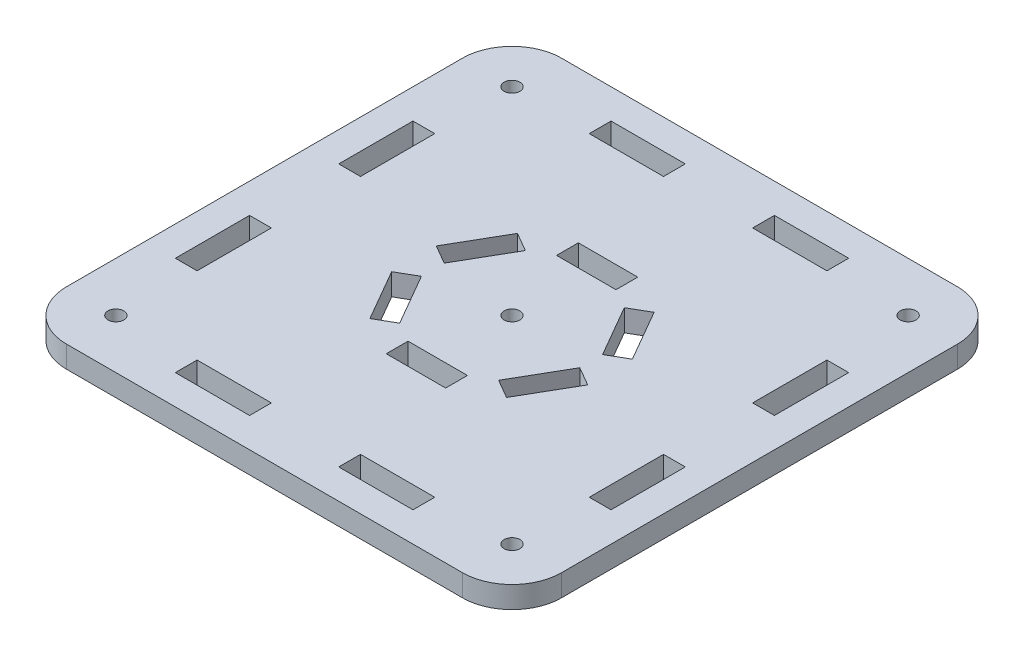
SolidWorks part; units mm, degrees
ref_plane "前视基准面" through (0, 0, 0) normal (0, 0, 1) x (1, 0, 0)
ref_plane "上视基准面" through (0, 0, 0) normal (0, 1, 0) x (1, 0, 0)
ref_plane "右视基准面" through (0, 0, 0) normal (1, 0, 0) x (0, 0, -1)
sketch "草图1" plane through (0, 0, 0) normal (0, 1, 0) x (1, 0, 0)
  line L1 (-50, -50) -> (50, -50)
  line L2 (-50, -50) -> (-50, 50)
  line L3 (-50, 50) -> (50, 50)
  line L4 (50, -50) -> (50, 50)
  line L5 (0, 50) -> (0, -50) construction
  line L6 (-50, 0) -> (50, 0) construction
  circle A0 centre (0, 0) radius 1.6
  point P0 (0, 0)
  dimension "D3" = 3.2
  dimension "D1" = 100
  dimension "D2" = 100
extrude "凸台-拉伸1" add sketch "草图1" along normal blind 4.4
fillet "圆角1" radius 10 4 edges at (50, 2.2, 50) (-50, 2.2, 50) (50, 2.2, -50) (-50, 2.2, -50)
sketch "草图2" plane through (0, 4.4, 0) normal (0, 1, 0) x (1, 0, 0)
  line L0 (0, 50) -> (0, 0) construction
  line L1 (40, 50) -> (-40, 50) construction
  line L2 (-24, 44) -> (-24, 39.6)
  line L3 (9, 44) -> (24, 44)
  line L4 (9, 44) -> (9, 39.6)
  line L5 (9, 39.6) -> (24, 39.6)
  line L6 (24, 44) -> (24, 39.6)
  line L7 (-9, 39.6) -> (-24, 39.6)
  line L8 (-9, 44) -> (-9, 39.6)
  line L9 (-9, 44) -> (-24, 44)
  line L10 (44, -9) -> (39.6, -9)
  line L11 (44, -9) -> (44, -24)
  line L12 (39.6, -9) -> (39.6, -24)
  line L13 (44, -24) -> (39.6, -24)
  line L14 (44, 9) -> (44, 24)
  line L15 (44, 24) -> (39.6, 24)
  line L16 (39.6, 9) -> (39.6, 24)
  line L17 (44, 9) -> (39.6, 9)
  line L18 (-9, -44) -> (-9, -39.6)
  line L19 (-9, -44) -> (-24, -44)
  line L20 (-9, -39.6) -> (-24, -39.6)
  line L21 (-24, -44) -> (-24, -39.6)
  line L22 (9, -44) -> (24, -44)
  line L23 (24, -44) -> (24, -39.6)
  line L24 (9, -39.6) -> (24, -39.6)
  line L25 (9, -44) -> (9, -39.6)
  line L26 (-44, 9) -> (-39.6, 9)
  line L27 (-44, 9) -> (-44, 24)
  line L28 (-39.6, 9) -> (-39.6, 24)
  line L29 (-44, 24) -> (-39.6, 24)
  line L30 (-44, -9) -> (-44, -24)
  line L31 (-44, -24) -> (-39.6, -24)
  line L32 (-39.6, -9) -> (-39.6, -24)
  line L33 (-44, -9) -> (-39.6, -9)
  circle A0 centre (40, 40) radius 1.6
  circle A1 centre (40, -40) radius 1.6
  circle A2 centre (-40, -40) radius 1.6
  circle A3 centre (-40, 40) radius 1.6
  point P40 (0, 0)
  point P50 (0, 0)
  dimension "D6" = 3.2
  dimension "D1" = 4.4
  dimension "D2" = 18
  dimension "D3" = 15
  dimension "D4" = 6
  dimension "D5" = 4
  dimension "D7" = 4
extrude "切除-拉伸1" cut sketch "草图2" against normal up to next
sketch "草图3" plane through (0, 4.4, 0) normal (0, 1, 0) x (1, 0, 0)
  line L0 (0, 15) -> (0, 0) construction
  line L1 (-6, 19.4) -> (6, 19.4)
  line L2 (-6, 19.4) -> (-6, 15)
  line L3 (-6, 15) -> (6, 15)
  line L4 (6, 19.4) -> (6, 15)
  line L5 (0, 15) -> (0, 19.4) construction
  line L6 (-6, 17.2) -> (6, 17.2) construction
  line L7 (13.8009, 14.8962) -> (9.9904, 12.6962)
  line L8 (9.9904, 12.6962) -> (15.9904, 2.3038)
  line L9 (19.8009, 4.5038) -> (15.9904, 2.3038)
  line L10 (13.8009, 14.8962) -> (19.8009, 4.5038)
  line L11 (19.8009, -4.5038) -> (15.9904, -2.3038)
  line L12 (15.9904, -2.3038) -> (9.9904, -12.6962)
  line L13 (13.8009, -14.8962) -> (9.9904, -12.6962)
  line L14 (19.8009, -4.5038) -> (13.8009, -14.8962)
  line L15 (6, -19.4) -> (6, -15)
  line L16 (6, -15) -> (-6, -15)
  line L17 (-6, -19.4) -> (-6, -15)
  line L18 (6, -19.4) -> (-6, -19.4)
  line L19 (-13.8009, -14.8962) -> (-9.9904, -12.6962)
  line L20 (-9.9904, -12.6962) -> (-15.9904, -2.3038)
  line L21 (-19.8009, -4.5038) -> (-15.9904, -2.3038)
  line L22 (-13.8009, -14.8962) -> (-19.8009, -4.5038)
  line L23 (-19.8009, 4.5038) -> (-15.9904, 2.3038)
  line L24 (-15.9904, 2.3038) -> (-9.9904, 12.6962)
  line L25 (-13.8009, 14.8962) -> (-9.9904, 12.6962)
  line L26 (-19.8009, 4.5038) -> (-13.8009, 14.8962)
  line L27 (9.9904, 12.6962) -> (8.6603, 15) construction
  line L29 (8.6603, 15) -> (6, 15) construction
  point P0 (0, 17.2)
  point P27 (0, 0)
  dimension "D1" = 4.4
  dimension "D2" = 12
  dimension "D3" = 15
  dimension "D4" = 6
extrude "切除-拉伸2" cut sketch "草图3" against normal through all
